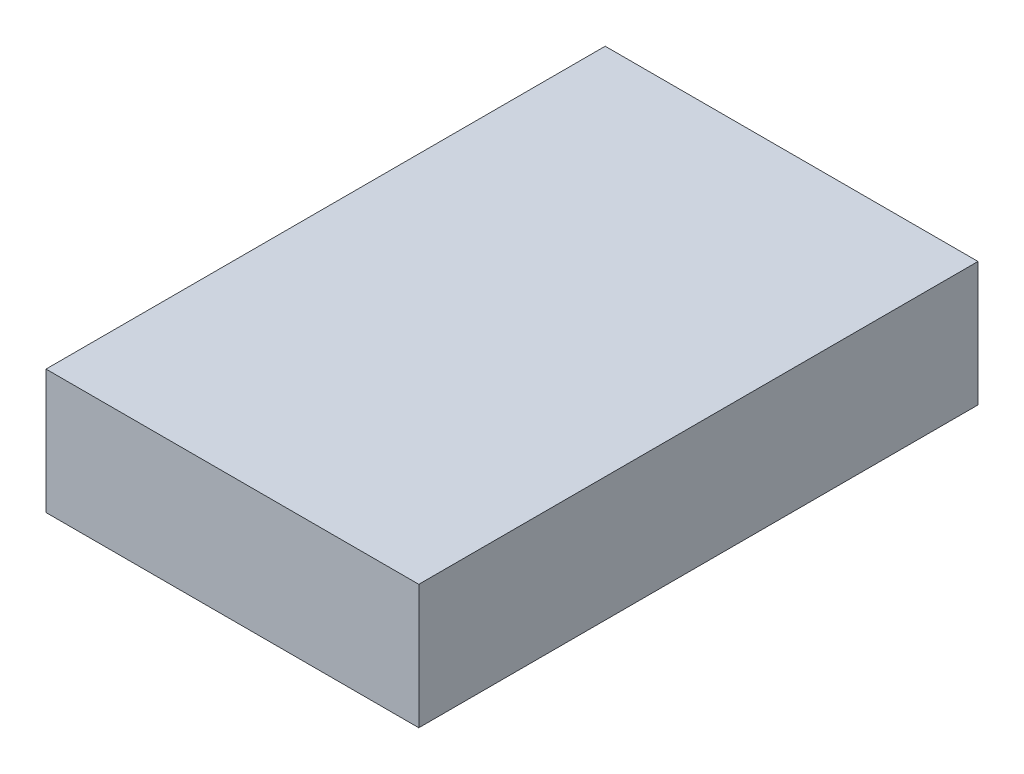
SolidWorks part; units mm, degrees
ref_plane "Front Plane" through (0, 0, 0) normal (0, 0, 1) x (1, 0, 0)
ref_plane "Top Plane" through (0, 0, 0) normal (0, 1, 0) x (1, 0, 0)
ref_plane "Right Plane" through (0, 0, 0) normal (1, 0, 0) x (0, 0, -1)
sketch "Sketch1" plane through (0, 0, 0) normal (0, 1, 0) x (1, 0, 0)
  line L1 (0, 0) -> (609.6, 0)
  line L2 (0, 0) -> (0, 914.4)
  line L3 (0, 914.4) -> (609.6, 914.4)
  line L4 (609.6, 0) -> (609.6, 914.4)
  dimension "D1" = 609.6
  dimension "D2" = 914.4
extrude "Boss-Extrude1" add sketch "Sketch1" along normal blind 203.2
